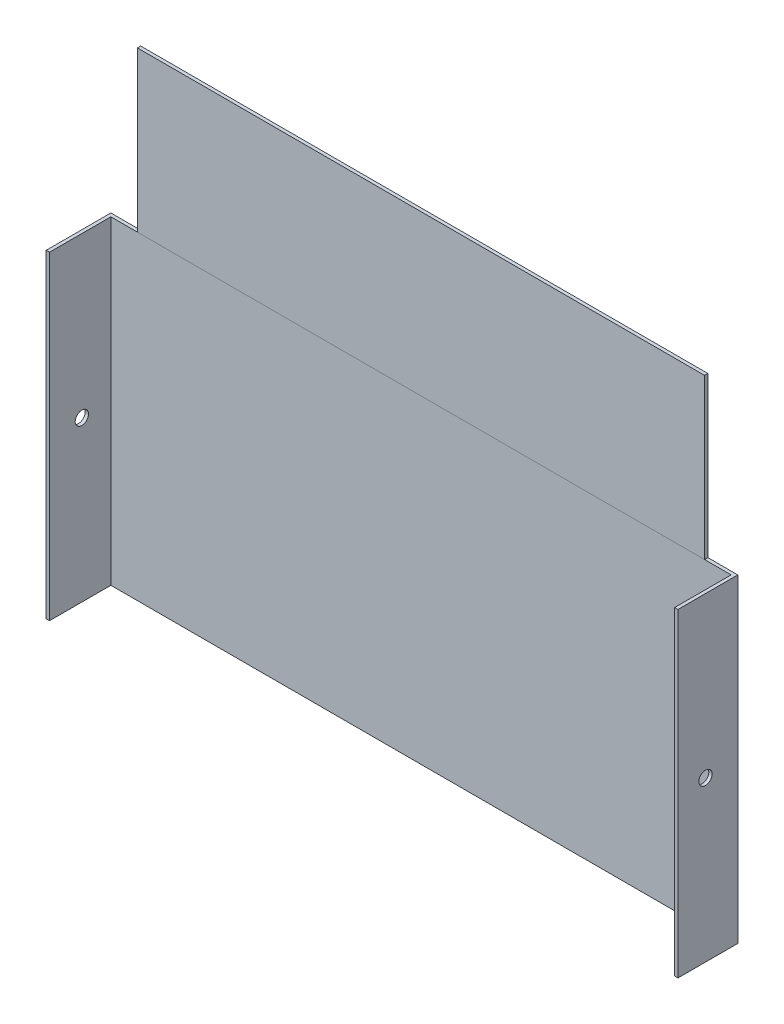
SolidWorks part; units mm, degrees
ref_plane "Front Plane" through (0, 0, 0) normal (0, 0, 1) x (1, 0, 0)
ref_plane "Top Plane" through (0, 0, 0) normal (0, 1, 0) x (1, 0, 0)
ref_plane "Right Plane" through (0, 0, 0) normal (1, 0, 0) x (0, 0, -1)
sketch "Sketch1" plane through (0, 0, 0) normal (0, 1, 0) x (1, 0, 0)
  line L0 (595.5063, 4.5679) -> (3.175, 4.5679)
  line L1 (0, 0) -> (0, 7.7429)
  line L2 (0, 0) -> (0, -53.975)
  line L3 (0, -53.975) -> (3.175, -53.975)
  line L4 (3.175, 4.5679) -> (3.175, -53.975)
  line L5 (0, 7.7429) -> (598.6813, 7.7429)
  line L6 (598.6813, 7.7429) -> (598.6813, 4.5679)
  line L7 (595.5063, 4.5679) -> (595.5063, -49.4071)
  line L8 (598.6813, -49.4071) -> (595.5063, -49.4071)
  line L11 (598.6813, 4.5679) -> (598.6813, -49.4071)
  dimension "D1" = 3.175
extrude "Boss-Extrude1" add sketch "Sketch1" along normal blind 304.8
sketch "Sketch2" plane through (0, 304.8, 0) normal (0, 1, 0) x (1, 0, 0)
  line L1 (54.0892, 54.0892) -> (544.5921, 54.0892)
  line L2 (54.0892, 54.0892) -> (54.0892, 50.9142)
  line L3 (54.0892, 50.9142) -> (544.5921, 50.9142)
  line L4 (544.5921, 54.0892) -> (544.5921, 50.9142)
sketch "Sketch3" plane through (0, 304.8, 0) normal (0, 1, 0) x (1, 0, 0)
  line L0 (3.175, 4.5679) -> (3.175, 7.7429)
  line L1 (598.6813, 7.7429) -> (0, 7.7429) construction
  line L2 (3.175, 7.7429) -> (595.5063, 7.7429)
  line L3 (595.5063, 7.7429) -> (595.5063, 4.5679)
  line L4 (3.175, 4.5679) -> (595.5063, 4.5679) construction
  line L5 (595.5063, 4.5679) -> (3.175, 4.5679)
sketch "Sketch4" plane through (0, 0, 0) normal (-1, 0, 0) x (0, 0, 1)
  line L0 (23.1161, 0) -> (23.1161, 304.8) construction
  line L1 (-7.7429, 0) -> (53.975, 0) construction
  line L2 (-7.7429, 304.8) -> (53.975, 304.8) construction
  circle A0 centre (23.1161, 152.4) radius 6.35
extrude "Cut-Extrude1" cut sketch "Sketch4" against normal through all
sketch "Sketch5" plane through (0, 304.8, 0) normal (0, 1, 0) x (1, 0, 0)
  line L0 (595.5063, 7.7429) -> (595.5063, 4.5679) construction
  line L1 (28.575, 7.6459) -> (570.1063, 7.6459)
  line L2 (28.575, 7.6459) -> (28.575, 4.5313)
  line L3 (28.575, 4.5313) -> (570.1063, 4.5313)
  line L4 (570.1063, 7.6459) -> (570.1063, 4.5313)
  line L5 (3.175, 4.5679) -> (3.175, 7.7429) construction
  dimension "D1" = 25.4
  dimension "D2" = 25.4
extrude "Boss-Extrude2" add sketch "Sketch5" along normal blind 152.4
